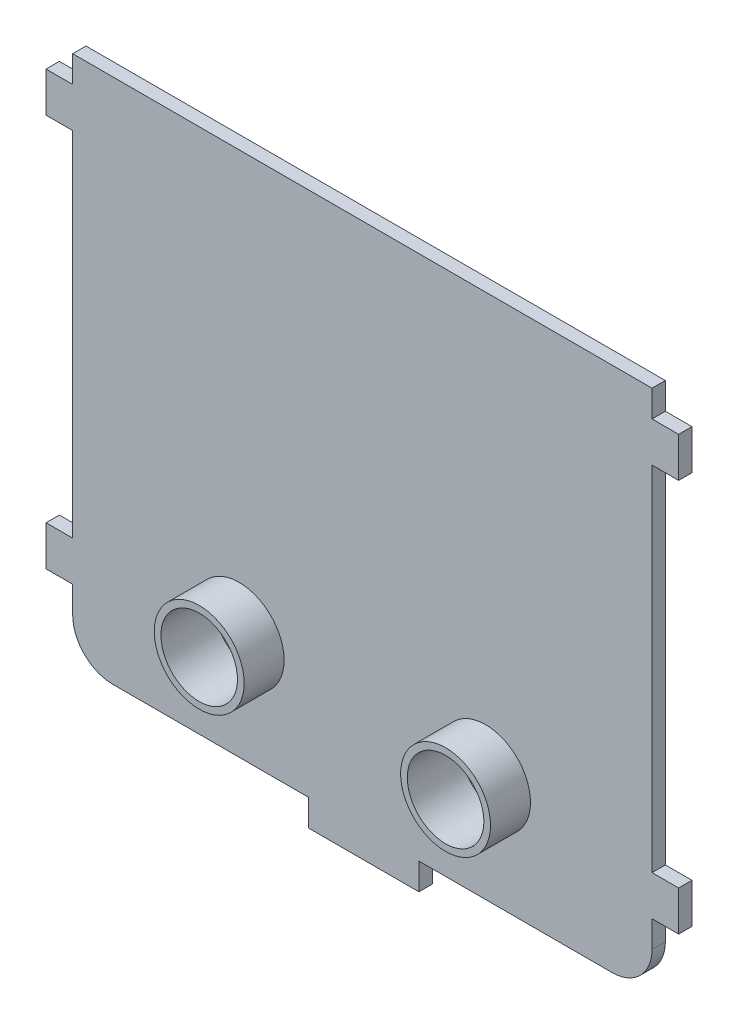
SolidWorks part; units mm, degrees
ref_plane "Front Plane" through (0, 0, 0) normal (0, 0, 1) x (1, 0, 0)
ref_plane "Top Plane" through (0, 0, 0) normal (0, 1, 0) x (1, 0, 0)
ref_plane "Right Plane" through (0, 0, 0) normal (1, 0, 0) x (0, 0, -1)
sketch "Sketch1" plane through (0, 0, 0) normal (0, 0, 1) x (1, 0, 0)
  line L1 (21.75, -19.75) -> (-21.75, -19.75)
  line L2 (21.75, -19.75) -> (21.75, 19.75)
  line L3 (21.75, 19.75) -> (-21.75, 19.75)
  line L4 (-21.75, -19.75) -> (-21.75, 19.75)
  line L5 (21.75, -19.75) -> (-21.75, 19.75) construction
  line L6 (21.75, 19.75) -> (-21.75, -19.75) construction
  point P0 (0, 0)
  dimension "D1" = 43.5
  dimension "D2" = 39.5
extrude "body" add sketch "Sketch1" along normal blind 1
sketch "Sketch2" plane through (21.75, 0, 0) normal (1, 0, 0) x (0, 0, -1)
  line L0 (-1, -19.75) -> (-1, 19.75) construction
  line L1 (-1, 17.75) -> (0, 17.75)
  line L2 (-1, 17.75) -> (-1, 14.75)
  line L3 (-1, 14.75) -> (0, 14.75)
  line L4 (0, 17.75) -> (0, 14.75)
  line L5 (0, -19.75) -> (0, 19.75) construction
  line L6 (-1, -19.75) -> (0, -19.75) construction
  line L7 (-1, -11.75) -> (0, -11.75)
  line L8 (-1, -11.75) -> (-1, -14.75)
  line L9 (-1, -14.75) -> (0, -14.75)
  line L10 (0, -11.75) -> (0, -14.75)
  line L11 (-1, 19.75) -> (0, 19.75) construction
  point P14 (-0.5, -14.75)
  point P17 (-0.5, 19.75)
  dimension "D1" = 26.5
  dimension "D2" = 5
  dimension "D3" = 3
  dimension "D4" = 3
  dimension "D5" = 2
extrude "clips_r" add sketch "Sketch2" along normal blind 2
sketch "Sketch3" plane through (-21.75, 0, 0) normal (-1, 0, 0) x (0, 0, 1)
  line L0 (1, 19.75) -> (0, 19.75) construction
  line L12 (0, 19.75) -> (0, -19.75) construction
  line L13 (0, -11.75) -> (1, -11.75)
  line L14 (0, -11.75) -> (0, -14.75)
  line L15 (0, -14.75) -> (1, -14.75)
  line L16 (1, -11.75) -> (1, -14.75)
  line L17 (1, 19.75) -> (1, -19.75) construction
  line L18 (1, -19.75) -> (0, -19.75) construction
  line L19 (0, 17.75) -> (1, 17.75)
  line L20 (0, 17.75) -> (0, 14.75)
  line L21 (0, 14.75) -> (1, 14.75)
  line L22 (1, 17.75) -> (1, 14.75)
  point P4 (0.5, 17.75)
  dimension "D1" = 5
  dimension "D2" = 3
  dimension "D3" = 26.5
  dimension "D4" = 3
  dimension "D5" = 2
extrude "clips_l" add sketch "Sketch3" along normal blind 2
sketch "Sketch4" plane through (0, -19.75, 0) normal (0, -1, 0) x (1, 0, 0)
  line L0 (-21.75, 1) -> (21.75, 1) construction
  line L1 (-4.0496, 1) -> (4.25, 1)
  line L2 (-4.0496, 1) -> (-4.0496, 0)
  line L3 (-4.0496, 0) -> (4.25, 0)
  line L4 (4.25, 1) -> (4.25, 0)
  line L5 (-21.75, 0) -> (21.75, 0) construction
  line L6 (21.75, 1) -> (21.75, 0) construction
  dimension "D1" = 8.2996
  dimension "D2" = 17.5
extrude "clips_b" add sketch "Sketch4" along normal blind 2
sketch "Sketch5" plane through (0, 0, 1) normal (0, 0, 1) x (1, 0, 0)
  line L0 (-21.75, -11.75) -> (21.75, -11.75) construction
  line L1 (-21.75, 14.75) -> (-21.75, -11.75) construction
  line L2 (21.75, -11.75) -> (21.75, 14.75) construction
  line L3 (-21.75, -19.75) -> (-4.0496, -19.75) construction
  line L4 (0.1002, -21.75) -> (0, -11.75) construction
  line L5 (4.25, -21.75) -> (-4.0496, -21.75) construction
  circle A1 centre (9.2505, -11.75) radius 3.375
  circle A2 centre (-9.2505, -11.75) radius 3.375
  dimension "D4" = 6.75
  dimension "D5" = 6.75
  dimension "D1" = 8
  dimension "D2" = 9.25
  dimension "D3" = 9.25
extrude "paddle_support" add sketch "Sketch5" along normal blind 3
sketch "Sketch6" plane through (0, 0, 4) normal (0, 0, 1) x (1, 0, 0)
  circle A0 centre (-9.2505, -11.75) radius 2.875
  circle A2 centre (9.2505, -11.75) radius 2.875
  dimension "D1" = 5.75
  dimension "D2" = 5.75
extrude "bolts" cut sketch "Sketch6" against normal through all
fillet "Fillet1" radius 3 2 edges at (-21.75, -19.75, 0.5) (21.75, -19.75, 0.5)
